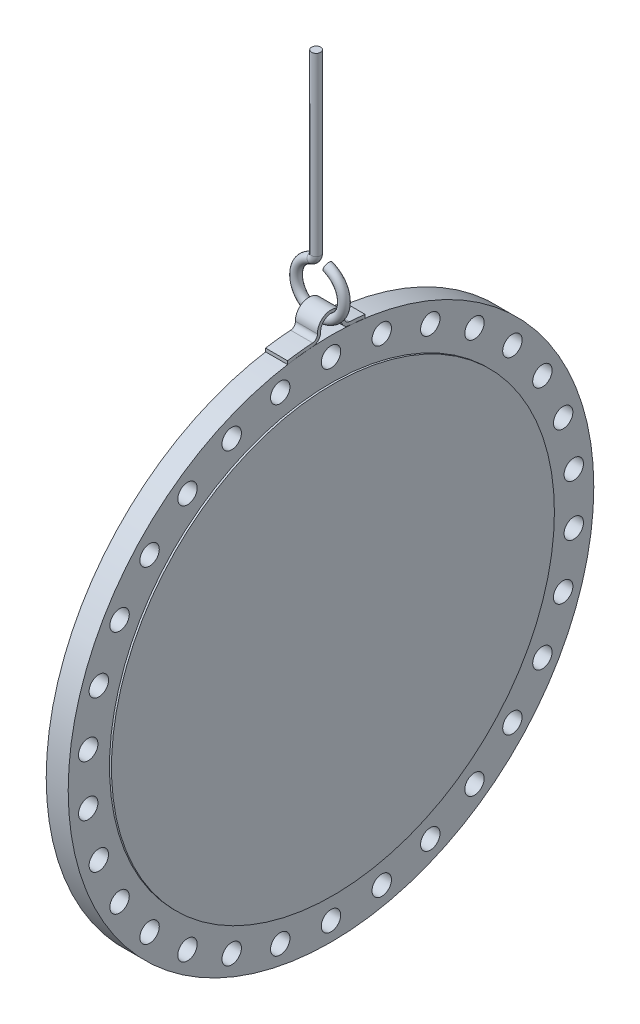
SolidWorks part; units mm, degrees
ref_plane "Front Plane" through (0, 0, 0) normal (0, 0, 1) x (1, 0, 0)
ref_plane "Top Plane" through (0, 0, 0) normal (0, 1, 0) x (1, 0, 0)
ref_plane "Right Plane" through (0, 0, 0) normal (1, 0, 0) x (0, 0, -1)
sketch "Sketch1" plane through (0, 0, 0) normal (0, 0, 1) x (1, 0, 0)
  line L0 (0, 342.5) -> (0, 0) construction
  line L1 (0, 0) -> (-488.3472, 0) construction
  line L2 (0, 0) -> (-37, 0)
  line L3 (-37, 0) -> (-37, 406.4)
  line L4 (-37, 406.4) -> (-3, 406.4)
  line L5 (-3, 406.4) -> (-3, 342.5)
  line L6 (-3, 342.5) -> (0, 342.5)
  line L7 (0, 342.5) -> (0, 0)
  dimension "D1" = 406.4
  dimension "D2" = 34
  dimension "D3" = 3
  dimension "D4" = 63.9
revolve "Revolve1" add sketch "Sketch1" angle 360 about L1
sketch "Sketch2" plane through (0, 0, 0) normal (1, 0, 0) x (0, 0, -1)
  circle A0 centre (0, 0) radius 377.5 construction
  circle A1 centre (0, 377.5) radius 15
  circle A2 centre (78.4867, 369.2507) radius 15
  circle A3 centre (153.5431, 344.8634) radius 15
  circle A4 centre (221.8889, 305.4039) radius 15
  circle A5 centre (280.5372, 252.5968) radius 15
  circle A6 centre (326.9246, 188.75) radius 15
  circle A7 centre (359.0238, 116.6539) radius 15
  circle A8 centre (375.432, 39.4595) radius 15
  circle A9 centre (375.432, -39.4595) radius 15
  circle A10 centre (359.0238, -116.6539) radius 15
  circle A11 centre (326.9246, -188.75) radius 15
  circle A12 centre (280.5372, -252.5968) radius 15
  circle A13 centre (221.8889, -305.4039) radius 15
  circle A14 centre (153.5431, -344.8634) radius 15
  circle A15 centre (78.4867, -369.2507) radius 15
  circle A16 centre (0, -377.5) radius 15
  circle A17 centre (-78.4867, -369.2507) radius 15
  circle A18 centre (-153.5431, -344.8634) radius 15
  circle A19 centre (-221.8889, -305.4039) radius 15
  circle A20 centre (-280.5372, -252.5968) radius 15
  circle A21 centre (-326.9246, -188.75) radius 15
  circle A22 centre (-359.0238, -116.6539) radius 15
  circle A23 centre (-375.432, -39.4595) radius 15
  circle A24 centre (-375.432, 39.4595) radius 15
  circle A25 centre (-359.0238, 116.6539) radius 15
  circle A26 centre (-326.9246, 188.75) radius 15
  circle A27 centre (-280.5372, 252.5968) radius 15
  circle A28 centre (-221.8889, 305.4039) radius 15
  circle A29 centre (-153.5431, 344.8634) radius 15
  circle A30 centre (-78.4867, 369.2507) radius 15
  point P65 (0, 0)
  dimension "D1" = 30
extrude "Cut-Extrude1" cut sketch "Sketch2" against normal up to next
sketch "Sketch3" plane through (-37, 0, 0) normal (-1, 0, 0) x (0, 0, 1)
  line L0 (0, 0) -> (0, 406.4) construction
  line L1 (-52.8312, 402.9514) -> (-52.8312, 407.9937)
  line L2 (67.1688, 400.8108) -> (67.1688, 405.8797)
  circle A0 centre (0, 0) radius 406.4 construction
  arc A1 (-28.0711, 405.4294) -> (-52.8312, 402.9514) centre (0, 0) ccw
  arc A2 (15.9902, 418.8393) -> (-15.9902, 418.8393) centre (0, 419.4) ccw
  arc A3 (-28.0711, 405.4294) -> (-15.9902, 418.8393) centre (-28.9681, 418.3843) ccw
  arc A4 (28.0711, 405.4294) -> (15.9902, 418.8393) centre (28.9681, 418.3843) cw
  arc A5 (20.9871, 418.6641) -> (-20.9871, 418.6641) centre (0, 419.4) ccw
  arc A6 (-28.4165, 410.4174) -> (-20.9871, 418.6641) centre (-28.9681, 418.3843) ccw
  arc A7 (-28.4165, 410.4174) -> (-52.8312, 407.9937) centre (0, 0) ccw
  arc A8 (28.4165, 410.4174) -> (20.9871, 418.6641) centre (28.9681, 418.3843) cw
  arc A9 (67.1688, 405.8797) -> (28.4165, 410.4174) centre (0, 0) ccw
  arc A10 (67.1688, 400.8108) -> (28.0711, 405.4294) centre (0, 0) ccw
  arc A11 (-28.4165, 410.4174) -> (28.4165, 410.4174) centre (0, 0) ccw construction
  arc A13 (-28.0711, 405.4294) -> (28.0711, 405.4294) centre (0, 0) ccw construction
  point P8 (67.1688, 400.8108)
  point P9 (-52.8312, 402.9514)
  dimension "D1" = 13
  dimension "D3" = 16
  dimension "D2" = 120
  dimension "D4" = 5
extrude "Boss-Extrude1" add sketch "Sketch3" against normal up to surface (34 mm away) separate body up to face at (-3, 369.2507, -93.4867)
sketch "Sketch4" plane through (0, 0, 0) normal (0, 0, 1) x (1, 0, 0)
  line L0 (-20, 440.4) -> (-20, 460.85) construction
  line L1 (-3, 440.4) -> (-37, 440.4) construction
  line L2 (-26, 505.0428) -> (-26, 777.3603)
  arc A0 (-32.5957, 495.64) -> (-8.4091, 495.9876) centre (-20, 460.85) ccw
  arc A1 (-32.5957, 495.64) -> (-26, 505.0428) centre (-36, 505.0428) ccw
  point P9 (0, 0)
  dimension "D2" = 37
  dimension "D3" = 10
  dimension "D1" = 20.45
  dimension "D4" = 6
ref_plane "Plane1" through (0, 777.3603, 0) normal (0, 1, 0) x (1, 0, 0)
sketch "Sketch5" plane through (0, 777.3603, 0) normal (0, 1, 0) x (1, 0, 0)
  line L0 (-57, 0) -> (17, 0) construction
  circle A0 centre (-26.0187, 0) radius 7
sweep "Sweep1" add profiles "Sketch5" path "Sketch4"
